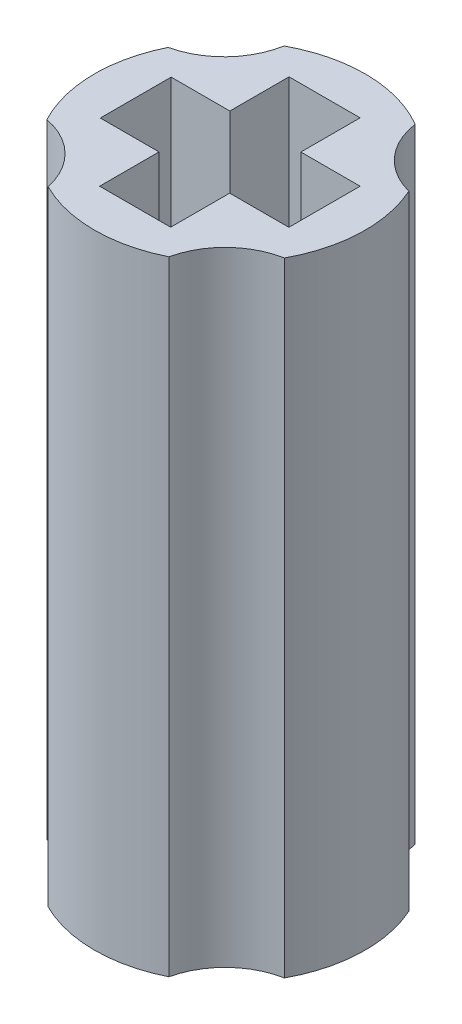
SolidWorks part; units mm, degrees
ref_plane "Front Plane" through (0, 0, 0) normal (0, 0, 1) x (1, 0, 0)
ref_plane "Top Plane" through (0, 0, 0) normal (0, 1, 0) x (1, 0, 0)
ref_plane "Right Plane" through (0, 0, 0) normal (1, 0, 0) x (0, 0, -1)
sketch "Sketch1" plane through (0, 0, 0) normal (0, 1, 0) x (1, 0, 0)
  line L0 (-0.9, -0.8953) -> (-0.9, -2.4)
  line L1 (-0.9, 2.4) -> (0.9, 2.4)
  line L2 (-0.9, 2.4) -> (-0.9, 0.9)
  line L3 (-0.9, -2.4) -> (0.9, -2.4)
  line L4 (0.9, 2.4) -> (0.9, 0.9)
  line L5 (-0.9, 2.4) -> (0.9, -2.4) construction
  line L6 (-0.9, -2.4) -> (0.9, 2.4) construction
  line L7 (-2.3874, -0.8953) -> (-0.9, -0.8953)
  line L8 (-2.3874, -0.8953) -> (-2.3874, 0.9)
  line L9 (-2.3874, 0.9) -> (-0.9, 0.9)
  line L10 (2.4, -0.9048) -> (2.4, 0.9)
  line L11 (-2.3874, -0.8953) -> (2.4, 0.9) construction
  line L12 (-2.3874, 0.9) -> (2.4, -0.9048) construction
  line L14 (0.9, 0.9) -> (2.4, 0.9)
  line L15 (0.9, -0.9048) -> (0.9, -2.4)
  line L16 (0.9, -0.9048) -> (2.4, -0.9048)
  arc A0 (-3.0781, 1.5134) -> (-3.0305, -1.6065) centre (0, 0) ccw
  arc A1 (3.0162, -1.6333) -> (1.5272, -3.0713) centre (3.3594, -3.4786) ccw
  arc A2 (-1.5416, -3.064) -> (-3.0305, -1.6065) centre (-3.3783, -3.451) ccw
  arc A3 (1.7379, 2.9571) -> (3.1279, 1.4076) centre (3.5956, 3.2254) ccw
  arc A4 (-3.0781, 1.5134) -> (-1.6402, 3.0124) centre (-3.4874, 3.3452) ccw
  arc A5 (1.7379, 2.9571) -> (-1.6402, 3.0124) centre (0, 0) ccw
  arc A6 (3.0162, -1.6333) -> (3.1279, 1.4076) centre (0, 0) ccw
  arc A7 (-1.5416, -3.064) -> (1.5272, -3.0713) centre (0, 0) ccw
  point P11 (0, 2.4)
  point P12 (0, 3.43)
  point P17 (-2.3874, 0.0024)
  point P19 (2.4, -0.0024)
  dimension "D1" = 1.03
  dimension "D2" = 3.56
  dimension "D3" = 3.56
  dimension "D4" = 3.56
  dimension "D5" = 3.56
extrude "Boss-Extrude1" add sketch "Sketch1" along normal blind 15.8
